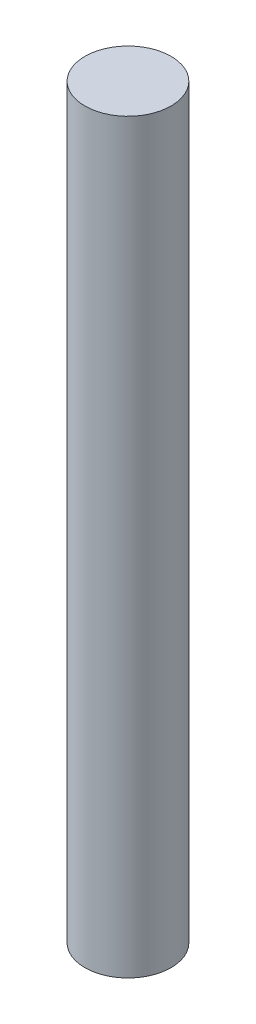
SolidWorks part; units mm, degrees
ref_plane "Front Plane" through (0, 0, 0) normal (0, 0, 1) x (1, 0, 0)
ref_plane "Top Plane" through (0, 0, 0) normal (0, 1, 0) x (1, 0, 0)
ref_plane "Right Plane" through (0, 0, 0) normal (1, 0, 0) x (0, 0, -1)
sketch "Sketch1" plane through (0, 0, 0) normal (0, 1, 0) x (1, 0, 0)
  circle A0 centre (0, 0) radius 1.905
  dimension "D1" = 3.81
extrude "Boss-Extrude1" add sketch "Sketch1" along normal blind 33.02
